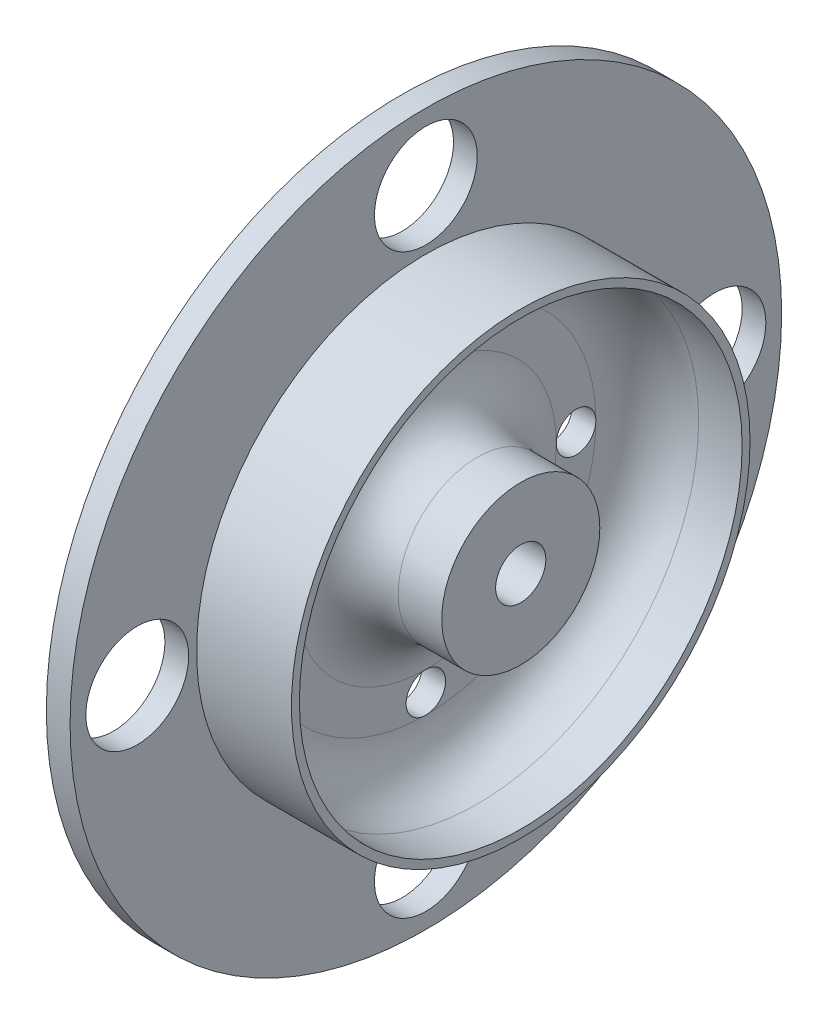
SolidWorks part; units mm, degrees
ref_plane "Front Plane" through (0, 0, 0) normal (0, 0, 1) x (1, 0, 0)
ref_plane "Top Plane" through (0, 0, 0) normal (0, 1, 0) x (1, 0, 0)
ref_plane "Right Plane" through (0, 0, 0) normal (1, 0, 0) x (0, 0, -1)
sketch "Sprocket" plane through (0, 0, 0) normal (1, 0, 0) x (0, 0, -1)
  circle A0 centre (0, 0) radius 45
  dimension "D1" = 90
extrude "Estrusione-Estrusione2" add sketch "Sprocket" along normal blind 3 contours A0
sketch "Schizzo4" plane through (3, 0, 0) normal (1, 0, 0) x (0, 0, -1)
  circle A0 centre (0, 0) radius 10
  dimension "D1" = 20
extrude "Estrusione-Estrusione4" add sketch "Schizzo4" along normal blind 12
sketch "Schizzo5" plane through (3, 0, 0) normal (1, 0, 0) x (0, 0, -1)
  circle A0 centre (0, 0) radius 28
  circle A1 centre (0, 0) radius 29
  circle A2 centre (0, 0) radius 45 construction
  dimension "D1" = 16
  dimension "D2" = 1
extrude "Estrusione-Estrusione5" add sketch "Schizzo5" along normal blind 12
sketch "Schizzo6" plane through (15, 0, 0) normal (1, 0, 0) x (0, 0, -1)
  circle A0 centre (0, 0) radius 3.175
  dimension "D1" = 6.35
extrude "Taglio-Estrusione1" cut sketch "Schizzo6" against normal up to surface (15 mm away) up to face at (0, 0, -45)
fillet "Raccordo1" radius 6.5 2 edges at (3, 0, -10) (3, 0, -28)
sketch "Schizzo7" plane through (3, 0, 0) normal (1, 0, 0) x (0, 0, -1)
  line L0 (0, 0) -> (0, 45) construction
  line L1 (0, 0) -> (45, 0) construction
  line L2 (0, 0) -> (0, -45) construction
  line L3 (0, 0) -> (-45, 0) construction
  circle A0 centre (0, 0) radius 45 construction
  circle A1 centre (0, 36.5) radius 6.5
  circle A2 centre (0, 0) radius 43 construction
  circle A3 centre (0, 0) radius 30 construction
  circle A4 centre (0, 0) radius 29 construction
  circle A5 centre (36.5, 0) radius 6.5
  circle A6 centre (0, -36.5) radius 6.5
  circle A7 centre (-36.5, 0) radius 6.5
  circle A8 centre (0, 19) radius 2.5
  circle A9 centre (0, 0) radius 21.5 construction
  circle A10 centre (0, 0) radius 16.5 construction
  circle A11 centre (19, 0) radius 2.5
  circle A12 centre (0, -19) radius 2.5
  circle A13 centre (-19, 0) radius 2.5
  point P21 (0, 0)
  point P37 (0, 0)
  dimension "D1" = 1
  dimension "D2" = 2
  dimension "D4" = 13
  dimension "D5" = 5
  dimension "D3" = 4
  dimension "D6" = 4
extrude "Taglio-Estrusione2" cut sketch "Schizzo7" against normal through all
scale "Scale1" scale about centroid uniform scaling yes scale factor 0.888889
equation "\"Thickness6\"=3"
equation "\"D1@Estrusione-Estrusione2\"=\"Thickness6\""
equation "\"D\"=90"
equation "\"D1@Sprocket\"=\"D\""
equation "\"Side_w\"=12"
equation "\"D1@Estrusione-Estrusione4\"=\"Side_w\""
equation "\"D1@Estrusione-Estrusione5\"=\"Side_w\""
